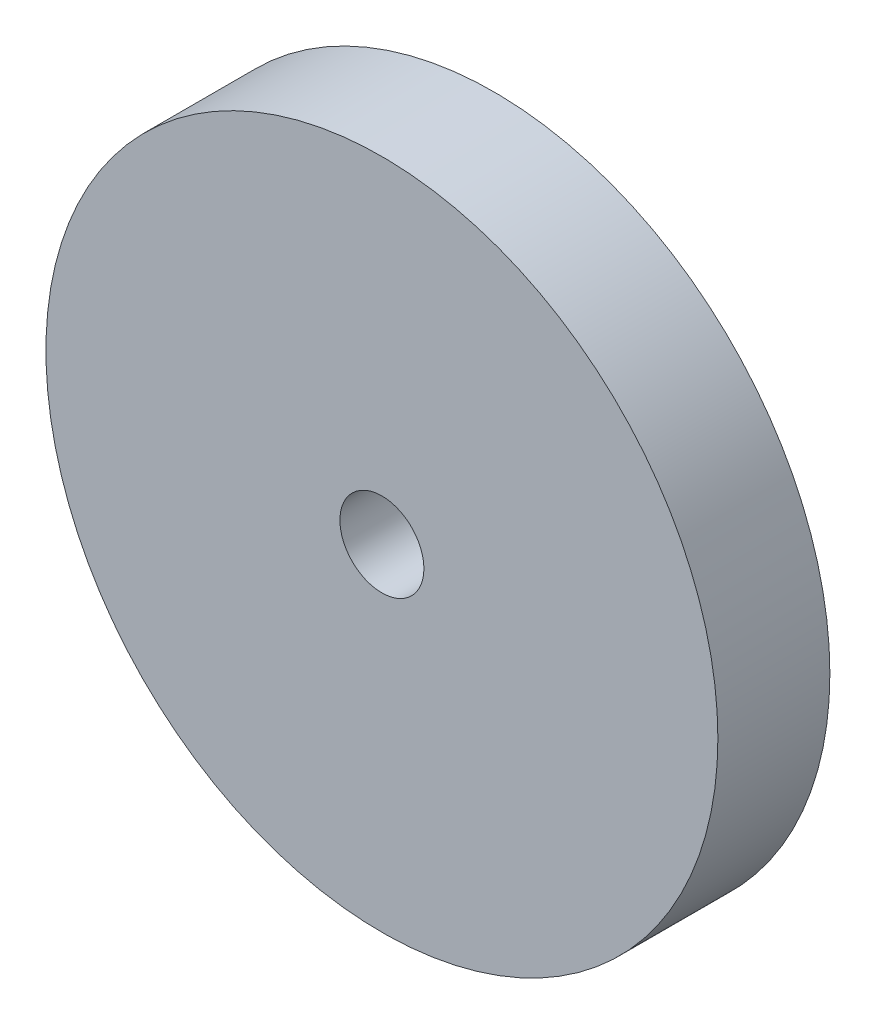
SolidWorks part; units mm, degrees
ref_plane "Front Plane" through (0, 0, 0) normal (0, 0, 1) x (1, 0, 0)
ref_plane "Top Plane" through (0, 0, 0) normal (0, 1, 0) x (1, 0, 0)
ref_plane "Right Plane" through (0, 0, 0) normal (1, 0, 0) x (0, 0, -1)
sketch "Sketch1" plane through (0, 0, 0) normal (0, 0, 1) x (1, 0, 0)
  circle A0 centre (0, 0) radius 76.2
  circle A1 centre (0, 0) radius 9.525
  dimension "D1" = 152.4
  dimension "D2" = 19.05
extrude "Boss-Extrude1" add sketch "Sketch1" along normal blind 25.4
sketch "Sketch2" plane through (0, 0, 0) normal (0, 0, 1) x (1, 0, 0)
  circle A0 centre (0, 0) radius 31.75
  dimension "D1" = 63.5
extrude "Boss-Extrude2" add sketch "Sketch2" against normal blind 22.225
